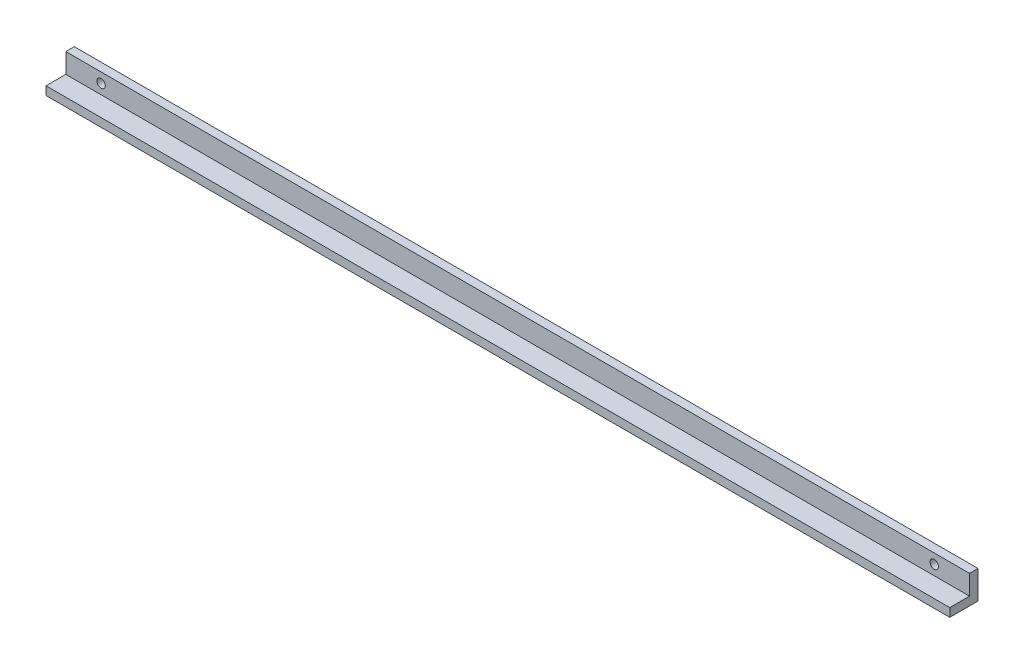
SolidWorks part; units mm, degrees
ref_plane "Спереди" through (0, 0, 0) normal (0, 0, 1) x (1, 0, 0)
ref_plane "Сверху" through (0, 0, 0) normal (0, 1, 0) x (1, 0, 0)
ref_plane "Справа" through (0, 0, 0) normal (1, 0, 0) x (0, 0, -1)
sketch "Эскиз1" plane through (0, 0, 0) normal (1, 0, 0) x (0, 0, -1)
  line L0 (0, 0) -> (-10, 0)
  line L1 (-10, 0) -> (-10, 3)
  line L2 (-10, 3) -> (-3, 3)
  line L3 (-3, 10) -> (-3, 3)
  line L6 (-3, 10) -> (0, 10)
  line L7 (0, 10) -> (0, 0)
  dimension "D1" = 3
  dimension "D2" = 10
extrude "Бобышка-Вытянуть1" add sketch "Эскиз1" along normal blind 320
sketch "Эскиз2" plane through (0, 0, 3) normal (0, 0, 1) x (1, 0, 0)
  line L0 (160, 10) -> (160, 3) construction
  line L1 (320, 10) -> (0, 10) construction
  line L2 (320, 3) -> (0, 3) construction
  line L3 (0, 10) -> (0, 3) construction
  circle A0 centre (12.5, 6.5) radius 1.5
  circle A1 centre (307.5, 6.5) radius 1.5
  dimension "D1" = 3
  dimension "D2" = 12.5
extrude "Вырез-Вытянуть1" cut sketch "Эскиз2" against normal through all
